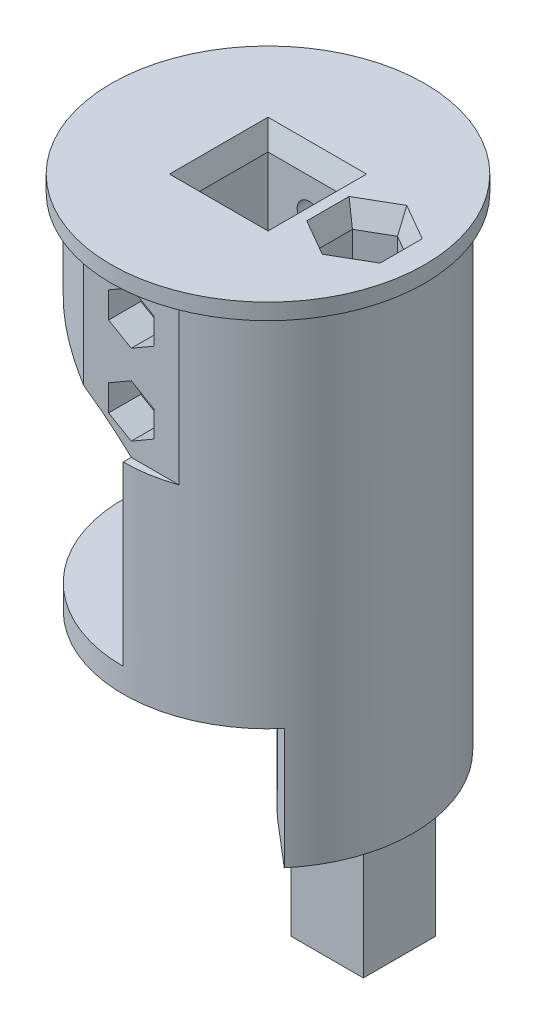
SolidWorks part; units mm, degrees
ref_plane "Спереди" through (0, 0, 0) normal (0, 0, 1) x (1, 0, 0)
ref_plane "Сверху" through (0, 0, 0) normal (0, 1, 0) x (1, 0, 0)
ref_plane "Справа" through (0, 0, 0) normal (1, 0, 0) x (0, 0, -1)
sketch "Эскиз1" plane through (0, 0, 0) normal (0, 1, 0) x (1, 0, 0)
  circle A0 centre (0, 0) radius 18
  dimension "D1" = 36
extrude "Бобышка-Вытянуть1" add sketch "Эскиз1" along normal blind 45
sketch "Эскиз2" plane through (0, 45, 0) normal (0, 1, 0) x (1, 0, 0)
  circle A0 centre (0, 0) radius 19.5
  dimension "D1" = 39
extrude "Бобышка-Вытянуть2" add sketch "Эскиз2" along normal blind 2
sketch "Эскиз3" plane through (0, 47, 0) normal (0, 1, 0) x (1, 0, 0)
  line L1 (-5.125, -5.125) -> (5.125, -5.125)
  line L2 (-5.125, -5.125) -> (-5.125, 5.125)
  line L3 (-5.125, 5.125) -> (5.125, 5.125)
  line L4 (5.125, -5.125) -> (5.125, 5.125)
  line L5 (-5.125, -5.125) -> (5.125, 5.125) construction
  line L6 (-5.125, 5.125) -> (5.125, -5.125) construction
  point P0 (0, 0)
  dimension "D1" = 10.25
extrude "Вырез-Вытянуть1" cut sketch "Эскиз3" against normal blind 40
sketch "Эскиз4" plane through (0, 0, 0) normal (0, -1, 0) x (1, 0, 0)
  line L0 (0, 0) -> (11.5702, 13.7888) construction
  line L1 (0, 0) -> (11.5702, -13.7888) construction
  line L2 (11.5702, 13.7888) -> (11.5702, -13.7888) construction
  line L3 (0, 0) -> (13.6996, 11.6756) construction
  line L5 (5.1423, -6.1284) -> (11.5702, -13.7888)
  line L6 (5.1423, -6.1284) -> (5.1423, 4.3826)
  line L7 (5.1423, 4.3826) -> (13.6996, 11.6756)
  circle A3 centre (0, 0) radius 18 construction
  arc A4 (13.6996, 11.6756) -> (11.5702, -13.7888) centre (0, 0) cw
  point P5 (11.5702, 13.7888)
  point P8 (11.5702, -13.7888)
  dimension "D1" = 100
  dimension "D2" = 3
  dimension "D3" = 10
extrude "Бобышка-Вытянуть3" add sketch "Эскиз4" along normal blind 15
sketch "Sketch1" plane through (0, -15, 0) normal (0, -1, 0) x (1, 0, 0)
  circle A0 centre (0, 0) radius 18
  arc A3 (13.6996, 11.6756) -> (11.5702, -13.7888) centre (0, 0) ccw construction
extrude "Boss-Extrude1" add sketch "Sketch1" along normal blind 20
sketch "Sketch3" plane through (0, -35, 0) normal (0, -1, 0) x (1, 0, 0)
  circle A0 centre (0, 0) radius 18
  circle A3 centre (0, 0) radius 18 construction
extrude "Boss-Extrude2" add sketch "Sketch3" along normal blind 7
sketch "Sketch4" plane through (0, -42, 0) normal (0, -1, 0) x (1, 0, 0)
  line L1 (5.1, 5.1) -> (-5.1, 5.1)
  line L2 (5.1, 5.1) -> (5.1, -5.1)
  line L3 (5.1, -5.1) -> (-5.1, -5.1)
  line L4 (-5.1, 5.1) -> (-5.1, -5.1)
  line L5 (5.1, 5.1) -> (-5.1, -5.1) construction
  line L6 (5.1, -5.1) -> (-5.1, 5.1) construction
  point P0 (0, 0)
  dimension "D1" = 10.2
  dimension "D2" = 10.2
extrude "Cut-Extrude2" cut sketch "Sketch4" against normal blind 27
sketch "Sketch6" plane through (0, 0, 0) normal (0, -1, 0) x (1, 0, 0)
  line L0 (0, 18) -> (0, -18) construction
  line L1 (0, 18) -> (0, -18)
  arc A0 (13.6996, 11.6756) -> (11.5702, -13.7888) centre (0, 0) ccw construction
  arc A1 (0, -18) -> (0, 18) centre (0, 0) cw
extrude "Cut-Extrude4" cut sketch "Sketch6" against normal blind 25
sketch "Sketch8" plane through (0, 0, 0) normal (0, -1, 0) x (1, 0, 0)
  line L0 (0, -18) -> (0, 18)
  arc A0 (0, -18) -> (0, 18) centre (0, 0) cw
  arc A1 (13.6996, 11.6756) -> (0, 18) centre (0, 0) ccw construction
extrude "Boss-Extrude3" add sketch "Sketch8" against normal blind 3
sketch "Sketch9" plane through (0, 0, 0) normal (-1, 0, 0) x (0, 0, 1)
  line L0 (-18, 3) -> (18, 25) construction
  line L2 (18, 25) -> (-18, 25)
  line L3 (18, 25) -> (18, 3)
  line L4 (18, 3) -> (-18, 3)
  line L5 (-18, 25) -> (-18, 3)
  line L6 (18, 25) -> (-18, 3) construction
  line L7 (18, 3) -> (-18, 25) construction
  point P4 (0, 14)
extrude "Cut-Extrude5" cut sketch "Sketch9" against normal blind 8
sketch "Sketch10" plane through (0, 0, 0) normal (0, -1, 0) x (1, 0, 0)
  line L0 (0, -18) -> (0, 18) construction
  line L2 (1.5, 8.7) -> (-1.5, 8.7)
  line L3 (1.5, 8.7) -> (1.5, 6.7)
  line L4 (1.5, 6.7) -> (-1.5, 6.7)
  line L5 (-1.5, 8.7) -> (-1.5, 6.7)
  line L6 (1.5, 8.7) -> (-1.5, 6.7) construction
  line L7 (1.5, 6.7) -> (-1.5, 8.7) construction
  circle A0 centre (0, 0) radius 3.7
  arc A1 (13.6996, 11.6756) -> (11.5702, -13.7888) centre (0, 0) ccw construction
  point P9 (0, 7.7)
  point P14 (0, 3.7)
  dimension "D1" = 7.4
  dimension "D2" = 2
  dimension "D3" = 3
  dimension "D4" = 4
extrude "Cut-Extrude6" cut sketch "Sketch10" against normal blind 10
sketch "Sketch11" plane through (0, -42, 0) normal (0, -1, 0) x (1, 0, 0)
  line L0 (-18, 0) -> (18, 0) construction
  circle A0 centre (0, 0) radius 18 construction
  circle A1 centre (12, 0) radius 2
  dimension "D1" = 4
  dimension "D2" = 6
extrude "Cut-Extrude7" cut sketch "Sketch11" against normal blind 102
sketch "Sketch15" plane through (0, -42, 0) normal (0, -1, 0) x (1, 0, 0)
  circle A0 centre (0, 0) radius 18
  circle A3 centre (0, 0) radius 18 construction
extrude "Cut-Extrude9" cut sketch "Sketch15" against normal blind 27
sketch "Sketch17" plane through (0, 25, 0) normal (0, -1, 0) x (1, 0, 0)
  line L2 (-18, 0) -> (14.8, 0) construction
  line L3 (14.8, 0) -> (13.8, 0) construction
  line L4 (0, 18) -> (0, -18) construction
  line L6 (5.9161, -17) -> (-5.9161, -17)
  line L7 (5.9161, 17) -> (-5.9161, 17)
  arc A0 (8, 16.1245) -> (8, -16.1245) centre (0, 0) ccw construction
  arc A1 (-5.9161, -17) -> (5.9161, -17) centre (0, 0) ccw
  arc A2 (-5.9161, 17) -> (5.9161, 17) centre (0, 0) cw
  point P14 (13.8, 0)
  point P20 (0, -17)
  point P23 (0, 17)
  dimension "D4" = 1
extrude "Cut-Extrude11" cut sketch "Sketch17" against normal up to surface (20 mm away) up to face at (0, 45, 18)
sketch "Sketch18" plane through (0, 0, -17) normal (0, 0, 1) x (1, 0, 0)
  line L0 (0, 25) -> (0, 45) construction
  line L1 (5.9161, 25) -> (-5.9161, 25) construction
  line L2 (5.9161, 45) -> (-5.9161, 45) construction
  line L3 (-1.5, 40) -> (-1.5, 30) construction
  line L4 (-1.5, 35) -> (1.5, 35) construction
  line L5 (1.5, 40) -> (1.5, 30) construction
  circle A0 centre (0, 30) radius 1.5
  circle A1 centre (0, 40) radius 1.5
  point P16 (0, 35)
  point P17 (0, 35)
  dimension "D1" = 3
  dimension "D3" = 10
extrude "Cut-Extrude12" cut sketch "Sketch18" along normal through all
sketch "Sketch19" plane through (0, 0, -17) normal (0, 0, 1) x (1, 0, 0)
  circle A0 centre (0, 30) radius 3
  circle A1 centre (0, 40) radius 3
  dimension "D1" = 6
extrude "Cut-Extrude13" cut sketch "Sketch19" along normal blind 3
sketch "Sketch23" plane through (0, 3, 0) normal (0, 1, 0) x (1, 0, 0)
  line L0 (0, 18) -> (0, -18) construction
  line L1 (0, -14.4) -> (8, -14.4)
  line L2 (8, 16.1245) -> (8, -16.1245) construction
  line L3 (0, 14.4) -> (8, 14.4)
  line L4 (0, -14.4) -> (0, -18)
  line L5 (0, 14.4) -> (0, 18)
  line L6 (8, -14.4) -> (8, -16.1245)
  line L7 (8, 16.1245) -> (8, 14.4)
  arc A0 (8, 16.1245) -> (8, -16.1245) centre (0, 0) ccw construction
  arc A1 (0, -18) -> (8, -16.1245) centre (0, 0) ccw
  arc A2 (0, 18) -> (8, 16.1245) centre (0, 0) cw
  arc A3 (-5.9161, 17) -> (-5.9161, -17) centre (0, 0) ccw construction
  arc A4 (11.5702, 13.7888) -> (13.6996, -11.6756) centre (0, 0) ccw construction
  dimension "D1" = 3.6
extrude "Boss-Extrude5" add sketch "Sketch23" along normal blind 22
sketch "Sketch25" plane through (0, 0, 17) normal (0, 0, 1) x (1, 0, 0)
  line L0 (-5.9161, 45) -> (-5.9161, 25) construction
  line L1 (-2.8146, 28.375) -> (0, 26.75)
  line L2 (0, 26.75) -> (2.8146, 28.375)
  line L3 (2.8146, 28.375) -> (2.8146, 31.625)
  line L4 (2.8146, 31.625) -> (0, 33.25)
  line L5 (0, 33.25) -> (-2.8146, 31.625)
  line L6 (-2.8146, 31.625) -> (-2.8146, 28.375)
  line L8 (-2.8146, 41.625) -> (-2.8146, 38.375)
  line L9 (-2.8146, 38.375) -> (0, 36.75)
  line L10 (0, 36.75) -> (2.8146, 38.375)
  line L11 (2.8146, 38.375) -> (2.8146, 41.625)
  line L12 (2.8146, 41.625) -> (0, 43.25)
  line L13 (0, 43.25) -> (-2.8146, 41.625)
  circle A0 centre (0, 30) radius 3.25 construction
  circle A1 centre (0, 40) radius 3.25 construction
  dimension "D1" = 6.5
extrude "Cut-Extrude16" cut sketch "Sketch25" against normal blind 4
sketch "Sketch26" plane through (0, 47, 0) normal (0, 1, 0) x (1, 0, 0)
  line L0 (14.8, 0) -> (5.125, 0) construction
  line L2 (8.4493, -2.05) -> (12, -4.1)
  line L3 (12, -4.1) -> (15.5507, -2.05)
  line L4 (15.5507, -2.05) -> (15.5507, 2.05)
  line L5 (15.5507, 2.05) -> (12, 4.1)
  line L6 (12, 4.1) -> (8.4493, 2.05)
  line L7 (5.125, -5.125) -> (5.125, 5.125) construction
  line L8 (8.4493, 2.05) -> (8.4493, -2.05)
  circle A0 centre (12, 0) radius 4.1 construction
  point P2 (15.5507, 0)
  dimension "D1" = 8.2
extrude "Cut-Extrude17" cut sketch "Sketch26" against normal blind 6
sketch "Sketch27" plane through (0, 0, 17) normal (0, 0, 1) x (1, 0, 0)
  line L0 (0, 25) -> (-20, 36.547) construction
  line L1 (-20, 36.547) -> (-20, 25)
  line L2 (-20, 25) -> (0, 25)
  line L3 (-18, 25) -> (-5.9161, 25) construction
  line L4 (-5.9161, 25) -> (0, 25) construction
  arc A0 (0, 25) -> (-20, 36.547) centre (-34.3242, -11.3572) ccw
  dimension "D3" = 50
  dimension "D1" = 30
  dimension "D2" = 20
extrude "Cut-Extrude18" cut sketch "Sketch27" against normal through all
fillet "Fillet2" radius 5 2 edges at (8, 14, 14.4) (8, 14, -14.4)
sketch "Sketch30" plane through (8, 0, 0) normal (-1, 0, 0) x (0, 0, 1)
  line L0 (-9.4, 8) -> (9.4, 8) construction
  line L1 (-9.4, 25) -> (-9.4, 3) construction
  line L2 (9.4, 3) -> (9.4, 25) construction
  line L4 (9.4, 13) -> (-9.4, 13)
  line L5 (9.4, 13) -> (9.4, 3)
  line L6 (9.4, 3) -> (-9.4, 3)
  line L7 (-9.4, 13) -> (-9.4, 3)
  line L8 (9.4, 13) -> (-9.4, 3) construction
  line L9 (9.4, 3) -> (-9.4, 13) construction
  point P6 (0, 8)
  dimension "D1" = 10
extrude "Cut-Extrude20" cut sketch "Sketch30" against normal blind 3
chamfer "Chamfer1" distance 1 angle 70 4 edges at (5.125, 47, 0) (0, 47, 5.125) (-5.125, 47, 0) (0, 47, -5.125)
chamfer "Chamfer2" distance 1 angle 70 6 edges at (15.5507, 47, 0) (13.7754, 47, 3.075) (13.7754, 47, -3.075) (10.2246, 47, -3.075) (8.4493, 47, 0) (10.2246, 47, 3.075)
sketch "Sketch37" plane through (0, -15, 0) normal (0, -1, 0) x (1, 0, 0)
  line L0 (5.1423, -0.8729) -> (17.9788, -0.8729) construction
  line L1 (5.1423, 4.3826) -> (5.1423, -6.1284) construction
  line L3 (15.4788, 3.6271) -> (6.4788, 3.6271)
  line L4 (15.4788, 3.6271) -> (15.4788, -5.3729)
  line L5 (15.4788, -5.3729) -> (6.4788, -5.3729)
  line L6 (6.4788, 3.6271) -> (6.4788, -5.3729)
  line L7 (15.4788, 3.6271) -> (6.4788, -5.3729) construction
  line L8 (15.4788, -5.3729) -> (6.4788, 3.6271) construction
  arc A0 (11.5702, -13.7888) -> (13.6996, 11.6756) centre (0, 0) ccw construction
  circle A1 centre (12, 0) radius 2
  point P8 (10.9788, -0.8729)
  dimension "D1" = 9
  dimension "D2" = 7
extrude "Boss-Extrude7" add sketch "Sketch37" along normal blind 15
sketch "Sketch38" plane through (0, -15, 0) normal (0, -1, 0) x (1, 0, 0)
  line L0 (5.1423, -6.1284) -> (5.1423, 4.3826)
  arc A0 (5.1423, -6.1284) -> (5.1423, 4.3826) centre (-10.9482, -0.8729) ccw
extrude "Cut-Extrude22" cut sketch "Sketch38" against normal up to surface (15 mm away) up to face at (0, 0, 7.7)
sketch "Sketch39" plane through (0, -15, 0) normal (0, -1, 0) x (1, 0, 0)
  line L0 (7.4207, -7.3729) -> (15.4207, -7.3729)
  line L1 (7.4207, -7.3729) -> (11.5989, -12.3522)
  line L2 (5.1423, -6.1284) -> (11.5702, -13.7888) construction
  line L3 (6.4788, -5.3729) -> (15.4788, -5.3729) construction
  line L4 (6.1866, -7.3729) -> (16.4207, -7.3729) construction
  arc A0 (11.5989, -12.3522) -> (15.4207, -7.3729) centre (-0.5503, 0.9293) ccw
  arc A1 (11.5702, -13.7888) -> (13.6996, 11.6756) centre (0, 0) ccw construction
  point P11 (11.4207, -7.3729)
  dimension "D1" = 8
  dimension "D2" = 2
  dimension "D3" = 6.5
  dimension "D4" = 5
  dimension "D6" = 50
extrude "Cut-Extrude23" cut sketch "Sketch39" against normal up to surface (28 mm away) up to face at (9.8333, 13, 0)
sketch "Sketch40" plane through (0, 3, 0) normal (0, 1, 0) x (1, 0, 0)
  line L0 (7.4207, 7.3729) -> (7.4207, 11.736)
  line L1 (7.4207, 11.736) -> (11.7839, 11.736)
  line L2 (11.7839, 11.736) -> (11.7839, 7.3729)
  line L3 (11.7839, 7.3729) -> (7.4207, 7.3729)
  line L4 (7.4207, 7.3729) -> (11, 7.3729) construction
  arc A1 (8, 9.4) -> (3, 14.4) centre (3, 9.4) ccw construction
extrude "Cut-Extrude24" cut sketch "Sketch40" along normal up to surface (10 mm away) up to face at (10.5956, 13, -3.0295)
fillet "Fillet7" radius 6 2 edges at (5.1423, -7.5, 4.3826) (5.1423, -7.5, -6.1284)
